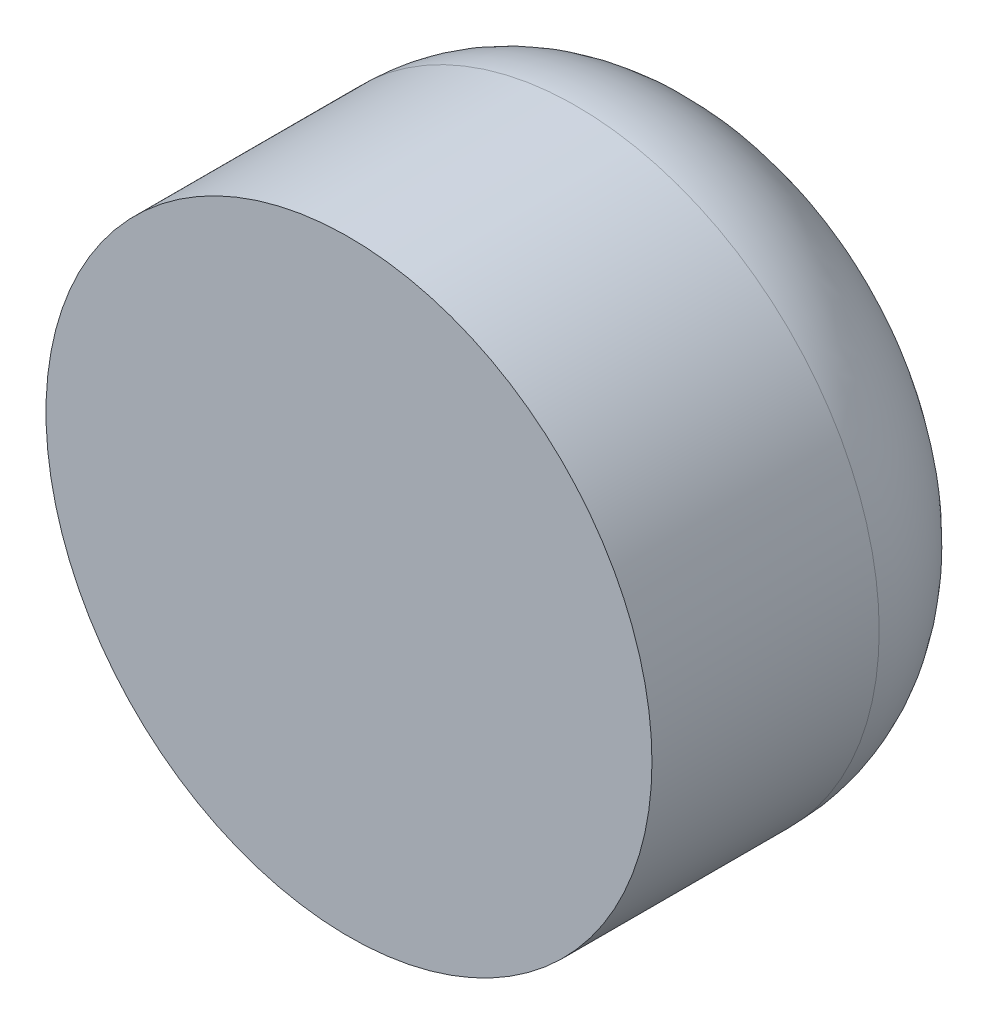
SolidWorks part; units mm, degrees
ref_plane "Front Plane" through (0, 0, 0) normal (0, 0, 1) x (1, 0, 0)
ref_plane "Top Plane" through (0, 0, 0) normal (0, 1, 0) x (1, 0, 0)
ref_plane "Right Plane" through (0, 0, 0) normal (1, 0, 0) x (0, 0, -1)
sketch "Sketch2" plane through (0, 0, 0) normal (0, 0, 1) x (1, 0, 0)
  circle A0 centre (0, 0) radius 4
extrude "Boss-Extrude1" add sketch "Sketch2" along normal blind 5
fillet "Fillet2" radius 2 1 edges at (4, 0, 0)
